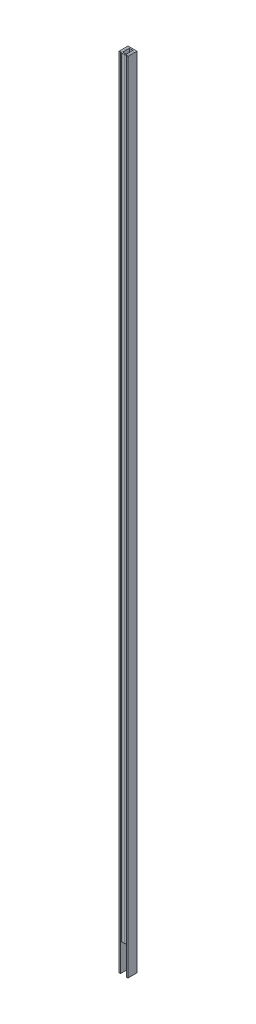
SolidWorks part; units mm, degrees
ref_plane "Front" through (0, 0, 0) normal (0, 0, 1) x (1, 0, 0)
ref_plane "Top" through (0, 0, 0) normal (0, 1, 0) x (1, 0, 0)
ref_plane "Right" through (0, 0, 0) normal (1, 0, 0) x (0, 0, -1)
sketch "Sketch1" plane through (0, 0, 0) normal (0, 1, 0) x (1, 0, 0)
  line L0 (-5, 0) -> (-7, 0)
  line L1 (-7, 0) -> (-7, 14)
  line L2 (-7, 14) -> (7, 14)
  line L4 (5, 12) -> (-5, 12)
  line L5 (-5, 12) -> (-5, 0)
  line L6 (5, 12) -> (5, 0)
  line L7 (7, 0) -> (7, 14)
  line L8 (5, 0) -> (7, 0)
  point P5 (0, 12)
  dimension "D1" = 14
  dimension "D2" = 2
  dimension "D3" = 2
extrude "Boss-Extrude1" add sketch "Sketch1" along normal blind 1260
sketch "Sketch2" plane through (0, 0, -12) normal (0, 0, 1) x (1, 0, 0)
  line L0 (-5, 0) -> (5, 0) construction
  circle A0 centre (0, 46) radius 3
  circle A1 centre (0, 11) radius 3
  dimension "D1" = 6
  dimension "D3" = 11
  dimension "D2" = 35
extrude "Fixing" cut sketch "Sketch2" against normal through all
sketch "Sketch4" plane through (0, 0, -12) normal (0, 0, 1) x (1, 0, 0)
  line L0 (-5, 0) -> (5, 0) construction
  line L1 (-2.5, 74.5) -> (2.5, 74.5)
  line L2 (-2.5, 74.5) -> (-2.5, 69.5)
  line L3 (-2.5, 69.5) -> (2.5, 69.5)
  line L4 (2.5, 74.5) -> (2.5, 69.5)
  line L5 (-2.5, 74.5) -> (2.5, 69.5) construction
  line L6 (-2.5, 69.5) -> (2.5, 74.5) construction
  point P0 (0, 72)
  point P5 (0, 0)
  dimension "D1" = 5
  dimension "D2" = 5
  dimension "D3" = 72
extrude "LED" add sketch "Sketch4" along normal blind 3
pattern_linear "LPattern1" count 72 spacing 16.6 along (0, 1, 0) of "LED"
sketch "Sketch3" plane through (0, 1260, 0) normal (0, 1, 0) x (1, 0, 0)
  line L0 (-5, 12) -> (-3, 12)
  line L1 (-5, 12) -> (5, 12) construction
  line L2 (-3, 12) -> (-3, 2.5)
  line L3 (-2, 1.5) -> (2, 1.5)
  line L4 (0, 1.5) -> (0, -0.5) construction
  line L5 (2, -0.5) -> (-2, -0.5)
  line L6 (-5, 0) -> (-5, 12) construction
  line L7 (-5, 2.5) -> (-5, 12)
  line L8 (5, 2.5) -> (5, 12)
  line L9 (3, 12) -> (3, 2.5)
  line L10 (5, 12) -> (3, 12)
  line L13 (-7, 0) -> (-5, 0) construction
  arc A0 (-3, 2.5) -> (-2, 1.5) centre (-2, 2.5) ccw
  arc A1 (-2, -0.5) -> (-5, 2.5) centre (-2, 2.5) cw
  arc A2 (2, -0.5) -> (5, 2.5) centre (2, 2.5) ccw
  arc A3 (3, 2.5) -> (2, 1.5) centre (2, 2.5) cw
  dimension "D1" = 0.5
  dimension "D2" = 3
  dimension "2" = 2
extrude "Diffuser" add sketch "Sketch3" against normal offset from surface (1215 mm away) 45 separate body up to face at (0, 0, -6.5)
